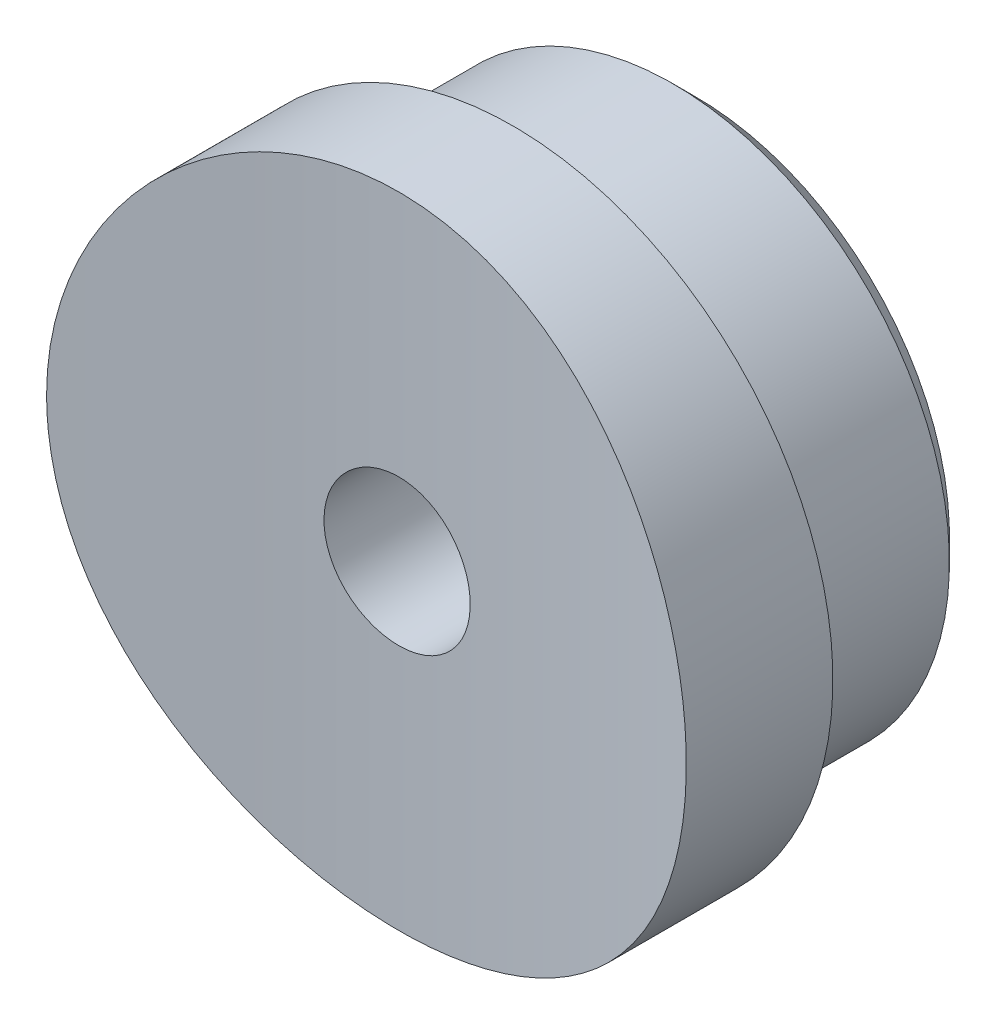
SolidWorks part; units mm, degrees
material "ABS"
ref_plane "Спереди" through (0, 0, 0) normal (0, 0, 1) x (1, 0, 0)
ref_plane "Сверху" through (0, 0, 0) normal (0, 1, 0) x (1, 0, 0)
ref_plane "Справа" through (0, 0, 0) normal (1, 0, 0) x (0, 0, -1)
sketch "Эскиз1" plane through (0, 0, 0) normal (0, 1, 0) x (1, 0, 0)
  line L1 (7, 2.5) -> (-7, 2.5)
  line L2 (7, 2.5) -> (7, -0.7071)
  line L4 (-7, 2.5) -> (-7, -0.7071)
  line L5 (1.5422, -0.034) -> (0, -0.75) construction
  line L6 (0, -0.75) -> (-1.5422, -0.034) construction
  arc A0 (7, -0.7071) -> (-7, -0.7071) centre (0, -35) ccw
  point P3 (0, -0.75)
  dimension "D1" = 70
  dimension "D4" = 2.5
extrude "Бобышка-Вытянуть1" add sketch "Эскиз1" along normal blind 14
sketch "Эскиз2" plane through (0, 0, -2.5) normal (0, 0, -1) x (-1, 0, 0)
  line L0 (-7, 14) -> (7, 14) construction
  line L1 (7, 14) -> (7, 0) construction
  line L2 (-7, 0) -> (7, 0) construction
  line L3 (-7, 14) -> (-7, 0) construction
  line L4 (-7, 14) -> (7, 14)
  line L5 (7, 14) -> (7, 0)
  line L6 (-7, 0) -> (7, 0)
  line L7 (-7, 14) -> (-7, 0)
  circle A0 centre (0, 7) radius 7
  line M2 (-7, 0) -> (7, 0)
  line M3 (7, 0) -> (7, 14)
  line M4 (7, 14) -> (-7, 14)
  line M5 (-7, 14) -> (-7, 0)
  dimension "D1" = 14
extrude "Вырез-Вытянуть3" cut sketch "Эскиз2" against normal blind 14 contours A0 L7 M2 | A0 L4 M5 | A0 L5 M4 | A0 L6 M3
sketch "Эскиз3" plane through (0, 0, -2.5) normal (0, 0, -1) x (-1, 0, 0)
  circle A0 centre (0, 7) radius 6.05
  dimension "D2" = 12.1
  dimension "D1" = 7
extrude "Бобышка-Вытянуть2" add sketch "Эскиз3" along normal blind 4
chamfer "Фаска1" distance 0.5 angle 45 1 edges at (-6.05, 7, -6.5)
sketch "Эскиз4" plane through (0, 0, -6.5) normal (0, 0, -1) x (-1, 0, 0)
  circle A0 centre (0, 7) radius 1.6
  dimension "D2" = 3.2
  dimension "D1" = 7
extrude "Вырез-Вытянуть4" cut sketch "Эскиз4" against normal through all
